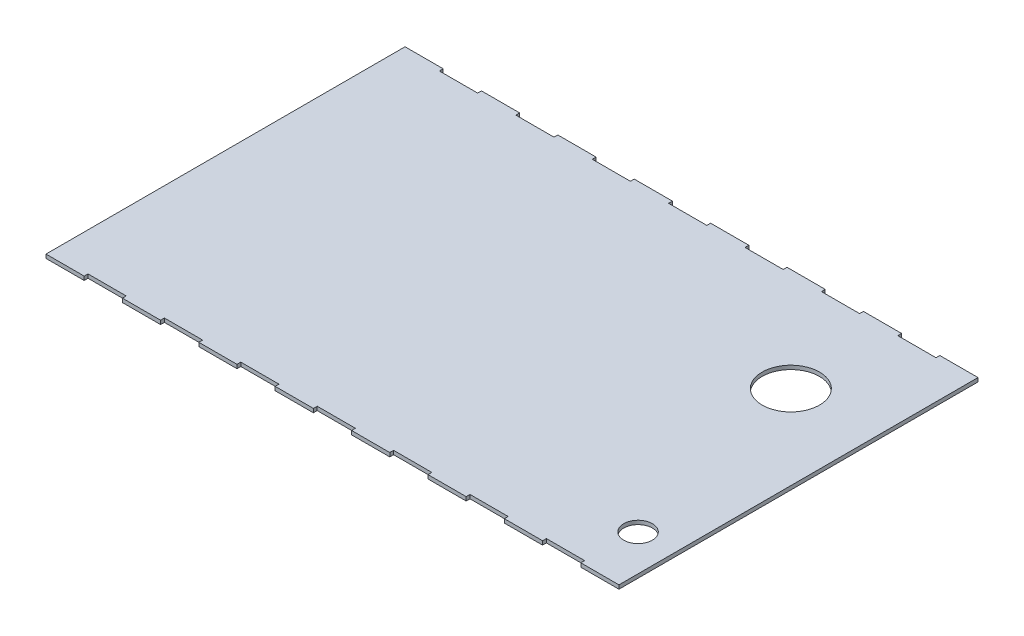
SolidWorks part; units mm, degrees
ref_plane "Front Plane" through (0, 0, 0) normal (0, 0, 1) x (1, 0, 0)
ref_plane "Top Plane" through (0, 0, 0) normal (0, 1, 0) x (1, 0, 0)
ref_plane "Right Plane" through (0, 0, 0) normal (1, 0, 0) x (0, 0, -1)
sketch "Sketch1" plane through (0, 0, 0) normal (0, 1, 0) x (1, 0, 0)
  line L1 (-224.2814, 65.7352) -> (75.7186, 65.7352)
  line L2 (-224.2814, 65.7352) -> (-224.2814, -122.2648)
  line L3 (-224.2814, -122.2648) -> (75.7186, -122.2648)
  line L4 (75.7186, 65.7352) -> (75.7186, -122.2648)
  dimension "D1" = 300
  dimension "D2" = 188
extrude "Boss-Extrude1" add sketch "Sketch1" along normal blind 2
sketch "Sketch2" plane through (0, 2, 0) normal (0, 1, 0) x (1, 0, 0)
  line L7 (-204.2814, -122.2648) -> (-184.2814, -122.2648)
  line L8 (-204.2814, -122.2648) -> (-204.2814, -120.2648)
  line L9 (-204.2814, -120.2648) -> (-184.2814, -120.2648)
  line L10 (-184.2814, -122.2648) -> (-184.2814, -120.2648)
  line L11 (-224.2814, -122.2648) -> (75.7186, -122.2648) construction
  line L12 (-224.2814, 65.7352) -> (-224.2814, -122.2648) construction
  dimension "D1" = 20
  dimension "D2" = 2
  dimension "D3" = 0
  dimension "D4" = 20
extrude "Cut-Extrude1" cut sketch "Sketch2" against normal blind 4
pattern_linear "LPattern1" count 8 spacing 40 along (1, 0, 0) of "Cut-Extrude1"
sketch "Sketch3" plane through (0, 2, 0) normal (0, 1, 0) x (1, 0, 0)
  line L0 (-98.9758, -28.2648) -> (53.2653, -28.2648)
  line L3 (-144.2814, -122.2648) -> (-124.2814, -122.2648) construction
  line L4 (75.7186, 65.7352) -> (-224.2814, 65.7352) construction
  dimension "D1" = 152.241
  dimension "D2" = 94
  dimension "D3" = 94
ref_plane "Plane1" through (0, 0, 28.2648) normal (0, 0, 1) x (1, 0, 0)
mirror "Mirror1" about plane through (0, 0, 28.2648) normal (0, 0, 1) of "LPattern1", "Cut-Extrude1"
sketch "Sketch4" plane through (0, 0, 0) normal (0, -1, 0) x (1, 0, 0)
  line L0 (15.7186, 122.2648) -> (35.7186, 122.2648) construction
  line L1 (75.7186, 122.2648) -> (75.7186, -65.7352) construction
  line L2 (75.7186, -65.7352) -> (55.7186, -65.7352) construction
  circle A0 centre (56.7186, 93.2648) radius 7.5
  circle A1 centre (31.7186, -11.7352) radius 15
  dimension "D1" = 29
  dimension "D5" = 15
  dimension "D6" = 30
  dimension "D2" = 19
  dimension "D3" = 44
  dimension "D4" = 54
extrude "Cut-Extrude2" cut sketch "Sketch4" against normal through all
